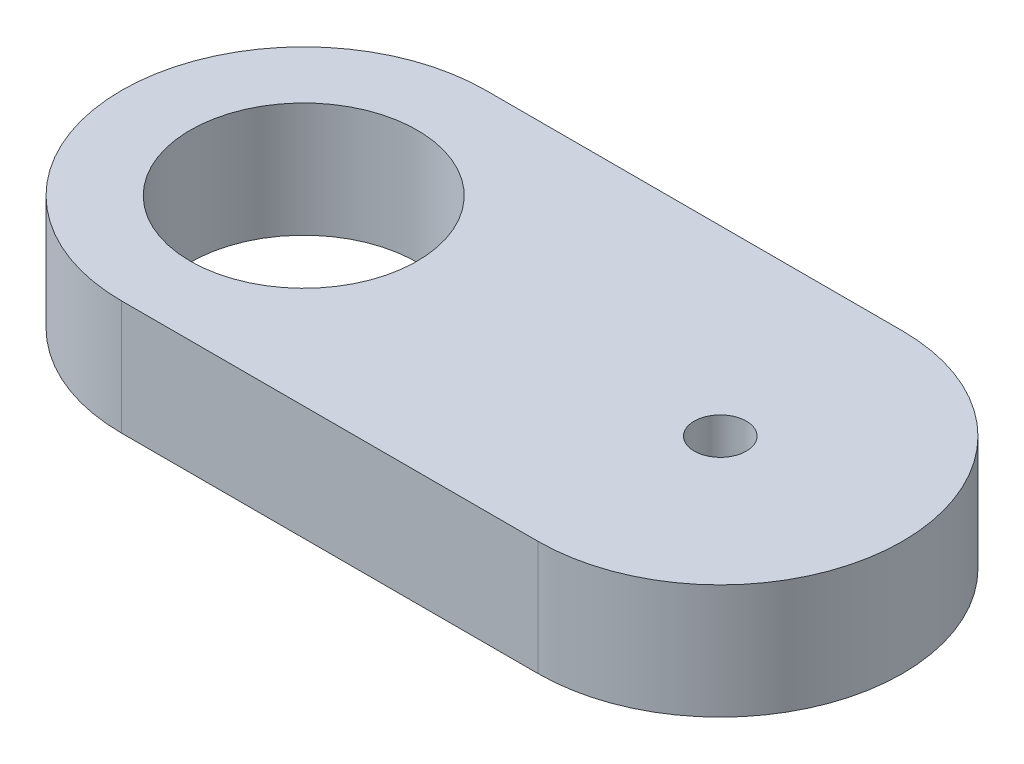
SolidWorks part; units mm, degrees
ref_plane "Front Plane" through (0, 0, 0) normal (0, 0, 1) x (1, 0, 0)
ref_plane "Top Plane" through (0, 0, 0) normal (0, 1, 0) x (1, 0, 0)
ref_plane "Right Plane" through (0, 0, 0) normal (1, 0, 0) x (0, 0, -1)
sketch "Sketch1" plane through (0, 0, 0) normal (0, 1, 0) x (1, 0, 0)
  line L0 (0, 0) -> (-40, 0) construction
  line L1 (-40, 7.5) -> (0, 10)
  line L2 (-40, -7.5) -> (0, -10)
  arc A0 (-1.2451, -9.9222) -> (-1.2451, 9.9222) centre (0, 0) ccw
  circle A1 centre (0, 0) radius 2.5
  circle A2 centre (-40, 0) radius 2
  arc A3 (-40, 7.5) -> (-40, -7.5) centre (-40, 0) ccw
  dimension "D1" = 5
  dimension "D2" = 20
  dimension "D4" = 4
  dimension "D5" = 15
  dimension "D3" = 40
extrude "Boss-Extrude1" add sketch "Sketch1" along normal blind 11
sketch "Sketch2" plane through (-0.6226, 0, -9.9611) normal (-0.0624, 0, -0.9981) x (-0.9981, 0, 0.0624)
  circle A0 centre (0, 6.09) radius 1.5
  dimension "D1" = 3
extrude "Cut-Extrude1" cut sketch "Sketch2" against normal up to vertex up to point (0, 0, 0)
sketch "Sketch3" plane through (0, 11, 0) normal (0, 1, 0) x (1, 0, 0)
  line L0 (-40, 17.5) -> (0, 17.5)
  line L1 (0, -17.5) -> (-40, -17.5)
  arc A0 (-40, 17.5) -> (-40, -17.5) centre (-40, 0) ccw
  circle A1 centre (-40, 0) radius 2
  circle A2 centre (0, 0) radius 2.5
  arc A3 (0, -17.5) -> (0, 17.5) centre (0, 0) ccw
  line M3 (0, 10) -> (-40, 7.5)
  arc M4 (-40, 7.5) -> (-40, -7.5) centre (-40, 0) ccw
  line M5 (-40, -7.5) -> (0, -10)
  arc M6 (0, -10) -> (0, 10) centre (0, 0) ccw
  dimension "D1" = 35
  dimension "D2" = 35
extrude "Boss-Extrude2" add sketch "Sketch3" against normal up to surface (11 mm away) contours L1 A3 L0 A0 M3 M6 M5 M4 up to face at (-40, 0, 2)
sketch "Sketch4" plane through (0, 11, 0) normal (0, 1, 0) x (1, 0, 0)
  circle A0 centre (-40, 0) radius 10.9
  dimension "D1" = 21.8
extrude "Cut-Extrude2" cut sketch "Sketch4" against normal blind 37.711
